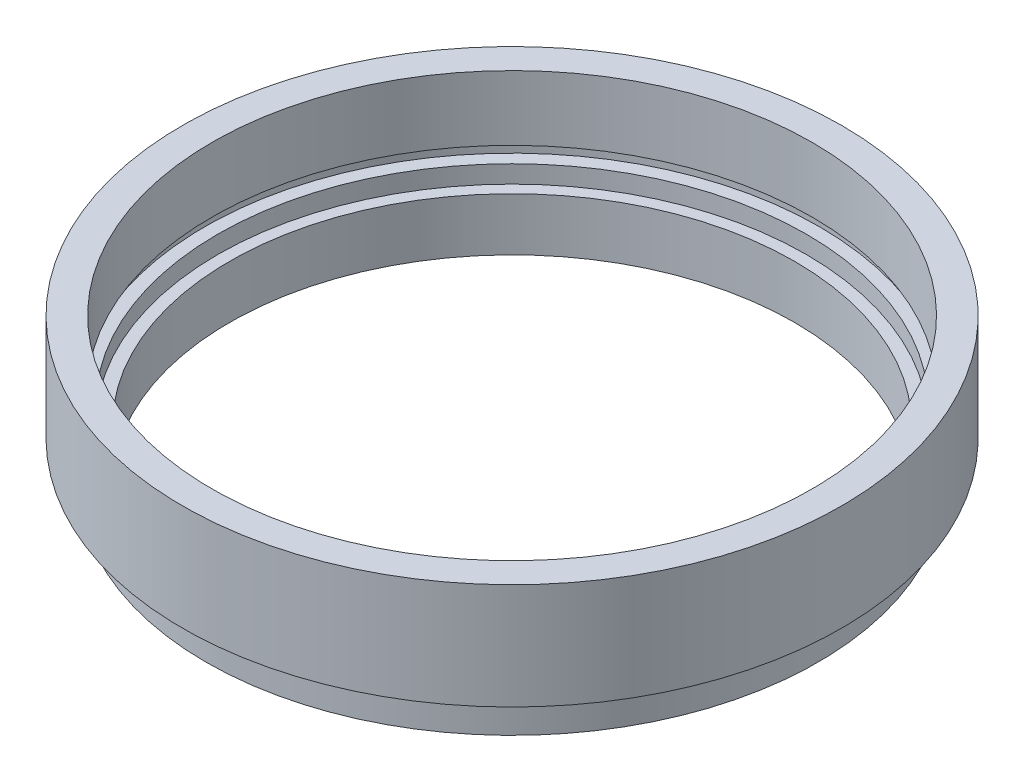
SolidWorks part; units mm, degrees
ref_plane "前视基准面" through (0, 0, 0) normal (0, 0, 1) x (1, 0, 0)
ref_plane "上视基准面" through (0, 0, 0) normal (0, 1, 0) x (1, 0, 0)
ref_plane "右视基准面" through (0, 0, 0) normal (1, 0, 0) x (0, 0, -1)
sketch "草图1" plane through (0, 0, 0) normal (0, 0, 1) x (1, 0, 0)
  line L0 (0, 0) -> (0, 21.8535) construction
  line L1 (24, 0) -> (26, 0)
  line L2 (26, 0) -> (26, 2.5)
  line L3 (26, 2.5) -> (25.5, 2.5)
  line L4 (25.5, 2.5) -> (25.5, 3.5)
  line L5 (25.5, 3.5) -> (28, 3.5)
  line L6 (28, 3.5) -> (28, 12.5)
  line L7 (28, 12.5) -> (25.5, 12.5)
  line L8 (25.5, 12.5) -> (25.5, 7)
  line L9 (25.5, 7) -> (26.1, 7)
  line L10 (26.1, 7) -> (26.1, 6)
  line L11 (26.1, 6) -> (25, 6)
  line L12 (25, 6) -> (25, 4.5)
  line L13 (25, 4.5) -> (24, 4.5)
  line L14 (24, 0) -> (24, 4.5)
  dimension "D1" = 12.5
  dimension "D2" = 28
  dimension "D3" = 25.5
  dimension "D4" = 25
  dimension "D5" = 1
  dimension "D6" = 1.5
  dimension "D7" = 24
  dimension "D8" = 26
  dimension "D9" = 1
  dimension "D10" = 3.5
  dimension "D11" = 4.5
  dimension "D12" = 26.1
  dimension "D13" = 25.5
revolve "旋转1" add sketch "草图1" angle 360 about L0
cosmetic thread "装饰螺纹线11" parameters "D2"=51
cosmetic thread "装饰螺纹线12" parameters "D2"=52
